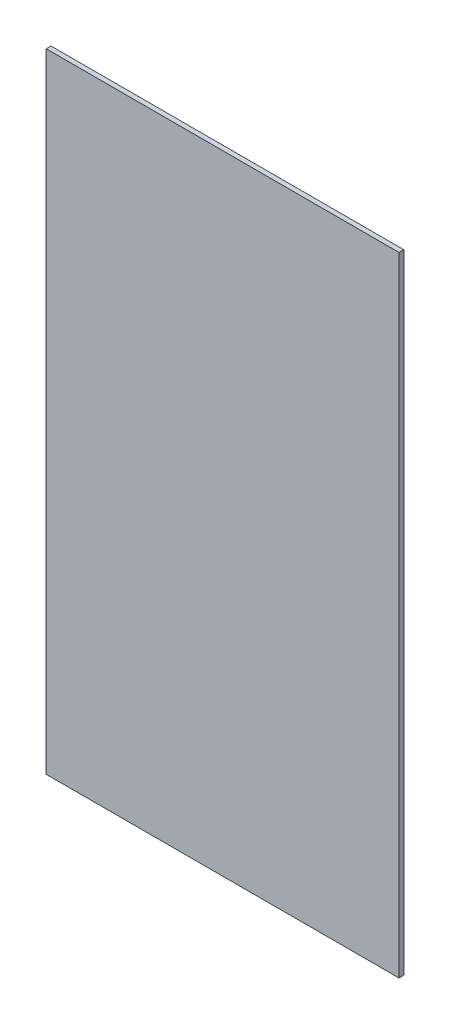
SolidWorks part; units mm, degrees
material "Plain Carbon Steel"
ref_plane "Front Plane" through (0, 0, 0) normal (0, 0, 1) x (1, 0, 0)
ref_plane "Top Plane" through (0, 0, 0) normal (0, 1, 0) x (1, 0, 0)
ref_plane "Right Plane" through (0, 0, 0) normal (1, 0, 0) x (0, 0, -1)
sketch "Sketch1" plane through (0, 0, 0) normal (0, 0, 1) x (1, 0, 0)
  line L1 (0, 0) -> (112.268, 0)
  line L2 (0, 0) -> (0, 200)
  line L3 (0, 200) -> (112.268, 200)
  line L4 (112.268, 0) -> (112.268, 200)
  dimension "D1" = 200
  dimension "D2" = 112.268
extrude "Bottom Outer Casing" add sketch "Sketch1" along normal blind 1.5189
